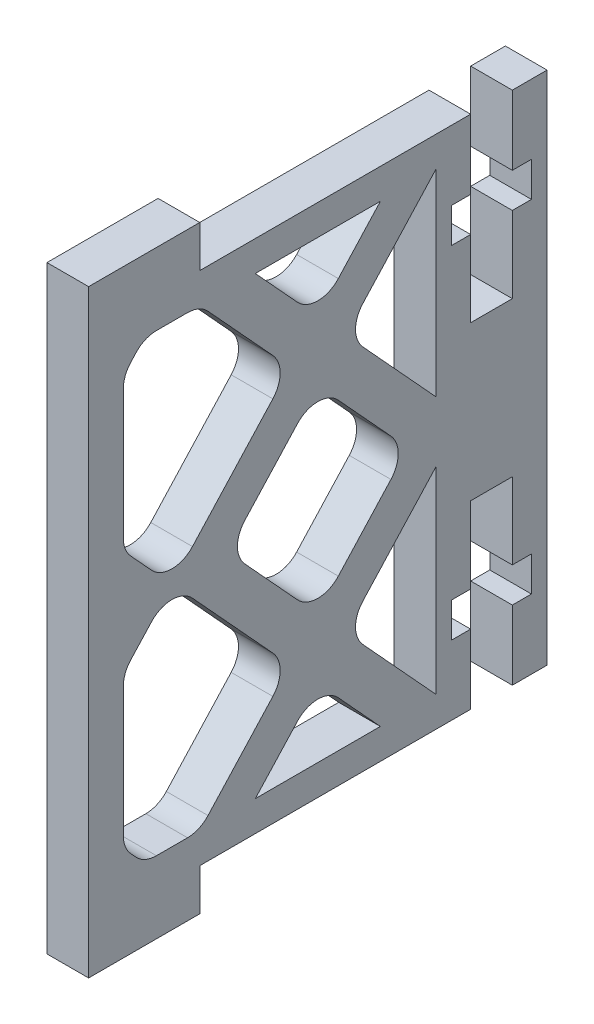
SolidWorks part; units mm, degrees
ref_plane "Plano frontal" through (0, 0, 0) normal (0, 0, 1) x (1, 0, 0)
ref_plane "Plano superior" through (0, 0, 0) normal (0, 1, 0) x (1, 0, 0)
ref_plane "Plano direito" through (0, 0, 0) normal (1, 0, 0) x (0, 0, -1)
sketch "Esboço1" plane through (0, 0, 0) normal (1, 0, 0) x (0, 0, -1)
  line L27 (-6.8934, 38.4024) -> (-6.8934, 41.4024)
  line L28 (-6.8934, 41.4024) -> (-14.8934, 41.4024)
  line L29 (-14.8934, 41.4024) -> (-14.8934, 38.4024)
  line L31 (-14.8934, 1.3024) -> (-14.8934, 38.4024)
  line L32 (16.9816, 30.9024) -> (16.9816, 33.4024)
  line L33 (12.6066, 38.4024) -> (12.6066, 33.4024)
  line L34 (12.6066, 25.4024) -> (15.6066, 25.4024)
  line L35 (15.6066, 25.4024) -> (15.6066, 30.9024)
  line L36 (11.2316, 30.9024) -> (12.6066, 30.9024)
  line L37 (16.9816, 33.4024) -> (15.6066, 33.4024)
  line L38 (11.2316, 33.4024) -> (11.2316, 30.9024)
  line L39 (12.6066, 33.4024) -> (11.2316, 33.4024)
  line L40 (12.6066, 30.9024) -> (12.6066, 25.4024)
  line L41 (15.6066, 30.9024) -> (16.9816, 30.9024)
  line L42 (12.6066, 33.4024) -> (11.2316, 33.4024)
  line L43 (18.1066, 38.4024) -> (18.1066, 1.3024)
  line L44 (9.5121, 4.1335) -> (10.1066, 3.4847)
  line L45 (12.6066, 38.4024) -> (-6.8934, 38.4024)
  line L46 (-1.6317, 11.9287) -> (-7.4189, 18.2435)
  line L47 (9.6066, 38.4024) -> (12.1066, 38.4024)
  line L48 (4.845, 27.7761) -> (10.1066, 22.0347)
  line L49 (0.1321, 14.3687) -> (-3.655, 18.5011)
  line L50 (15.6066, 1.3024) -> (18.1066, 1.3024)
  line L51 (15.6066, 6.3024) -> (15.6066, 1.3024)
  line L52 (-11.8679, 16.6067) -> (-10.3679, 18.2435)
  line L53 (-11.4879, 4.1335) -> (-11.8679, 4.5481)
  line L54 (9.5121, 35.5713) -> (10.1066, 36.22)
  line L55 (6.1066, 3.4847) -> (3.0811, 6.7861)
  line L56 (9.5121, 4.1335) -> (4.845, 9.2261)
  line L57 (-6.2989, 4.1335) -> (-1.6317, 9.2261)
  line L58 (-2.8934, 3.4847) -> (0.1321, 6.7861)
  line L59 (3.0811, 14.3687) -> (6.8683, 18.5011)
  line L60 (-2.8934, 3.4847) -> (6.1066, 3.4847)
  line L61 (12.6066, 38.4024) -> (10.1066, 38.4024)
  line L62 (-12.3934, 24.4493) -> (-12.3934, 33.8055)
  line L63 (10.1066, 17.67) -> (10.1066, 1.3024)
  line L64 (-10.0134, 36.22) -> (-7.7733, 36.22)
  line L65 (-2.8934, 36.22) -> (6.1066, 36.22)
  line L67 (3.0811, 25.3361) -> (6.8683, 21.2037)
  line L69 (-10.0134, 3.4847) -> (-7.7733, 3.4847)
  line L70 (-2.8934, 36.22) -> (0.1321, 32.9187)
  line L71 (-6.2989, 35.5713) -> (-1.6317, 30.4787)
  line L72 (9.5121, 35.5713) -> (4.845, 30.4787)
  line L73 (6.1066, 36.22) -> (3.0811, 32.9187)
  line L75 (-11.4879, 35.5713) -> (-11.8679, 35.1567)
  line L76 (10.1066, 38.4024) -> (10.1066, 22.0347)
  line L79 (-11.8679, 23.0981) -> (-10.3679, 21.4613)
  line L89 (15.6066, 33.4024) -> (15.6066, 38.4024)
  line L90 (15.6066, 38.4024) -> (18.1066, 38.4024)
  line L91 (12.6066, 1.3024) -> (10.1066, 1.3024)
  line L92 (4.845, 11.9287) -> (10.1066, 17.67)
  line L93 (9.6066, 1.3024) -> (12.1066, 1.3024)
  line L94 (-12.3934, 5.8993) -> (-12.3934, 15.2555)
  line L95 (12.6066, 1.3024) -> (-6.8934, 1.3024)
  line L97 (0.1321, 25.3361) -> (-3.655, 21.2037)
  line L98 (12.6066, 6.3024) -> (11.2316, 6.3024)
  line L99 (-1.6317, 27.7761) -> (-7.4189, 21.4613)
  line L100 (15.6066, 8.8024) -> (16.9816, 8.8024)
  line L101 (12.6066, 8.8024) -> (12.6066, 14.3024)
  line L102 (12.6066, 6.3024) -> (11.2316, 6.3024)
  line L103 (11.2316, 6.3024) -> (11.2316, 8.8024)
  line L104 (16.9816, 6.3024) -> (15.6066, 6.3024)
  line L105 (11.2316, 8.8024) -> (12.6066, 8.8024)
  line L106 (15.6066, 14.3024) -> (15.6066, 8.8024)
  line L107 (12.6066, 14.3024) -> (15.6066, 14.3024)
  line L108 (12.6066, 1.3024) -> (12.6066, 6.3024)
  line L109 (16.9816, 8.8024) -> (16.9816, 6.3024)
  line L110 (-14.8934, -1.6976) -> (-14.8934, 1.3024)
  line L111 (-6.8934, -1.6976) -> (-14.8934, -1.6976)
  line L112 (-6.8934, 1.3024) -> (-6.8934, -1.6976)
  arc A15 (-1.6317, 27.7761) -> (-1.6317, 30.4787) centre (-3.1062, 29.1274) ccw
  arc A16 (4.845, 27.7761) -> (4.845, 30.4787) centre (6.3194, 29.1274) cw
  arc A17 (0.1321, 25.3361) -> (3.0811, 25.3361) centre (1.6066, 23.9849) cw
  arc A18 (0.1321, 32.9187) -> (3.0811, 32.9187) centre (1.6066, 34.2699) ccw
  arc A23 (6.8683, 18.5011) -> (6.8683, 21.2037) centre (5.3938, 19.8524) ccw
  arc A24 (-3.655, 18.5011) -> (-3.655, 21.2037) centre (-2.1806, 19.8524) cw
  arc A25 (0.1321, 14.3687) -> (3.0811, 14.3687) centre (1.6066, 15.7199) ccw
  arc A26 (-1.6317, 9.2261) -> (-1.6317, 11.9287) centre (-3.1062, 10.5774) ccw
  arc A27 (3.0811, 6.7861) -> (0.1321, 6.7861) centre (1.6066, 5.4349) ccw
  arc A28 (4.845, 11.9287) -> (4.845, 9.2261) centre (6.3194, 10.5774) ccw
  arc A30 (-7.7733, 3.4847) -> (-6.2989, 4.1335) centre (-7.7733, 5.4847) ccw
  arc A31 (-11.4879, 4.1335) -> (-10.0134, 3.4847) centre (-10.0134, 5.4847) ccw
  arc A32 (-12.3934, 5.8993) -> (-11.8679, 4.5481) centre (-10.3934, 5.8993) ccw
  arc A33 (-12.3934, 15.2555) -> (-11.8679, 16.6067) centre (-10.3934, 15.2555) cw
  arc A34 (-7.4189, 18.2435) -> (-10.3679, 18.2435) centre (-8.8934, 16.8922) ccw
  arc A35 (-7.4189, 21.4613) -> (-10.3679, 21.4613) centre (-8.8934, 22.8126) cw
  arc A36 (-7.7733, 36.22) -> (-6.2989, 35.5713) centre (-7.7733, 34.22) cw
  arc A37 (-11.4879, 35.5713) -> (-10.0134, 36.22) centre (-10.0134, 34.22) cw
  arc A38 (-11.8679, 35.1567) -> (-12.3934, 33.8055) centre (-10.3934, 33.8055) ccw
  arc A39 (-11.8679, 23.0981) -> (-12.3934, 24.4493) centre (-10.3934, 24.4493) cw
  point P5 (3.6066, 29.1274)
  point P9 (1.6066, 26.945)
  point P25 (12.1066, 19.8524)
  point P65 (-8.8934, 19.8524)
  point P73 (-12.3934, 19.8524)
  point P102 (-12.3934, 23.6715)
  point P108 (10.1066, 36.22)
  point P127 (18.1066, 19.8524)
  dimension "D1" = 2
  dimension "D2" = 2
  dimension "D3" = 2
  dimension "D4" = 2
  dimension "D9" = 2
  dimension "D10" = 2
  dimension "D11" = 2
  dimension "D12" = 2
  dimension "D13" = 2
  dimension "D14" = 2
  dimension "D16" = 2
  dimension "D17" = 2
  dimension "D18" = 2
  dimension "D19" = 2
  dimension "D20" = 2
  dimension "D21" = 2
  dimension "D22" = 2
  dimension "D23" = 2
  dimension "D24" = 2
  dimension "D25" = 2
extrude "Ressalto-extrusão1" add sketch "Esboço1" along normal blind 3
